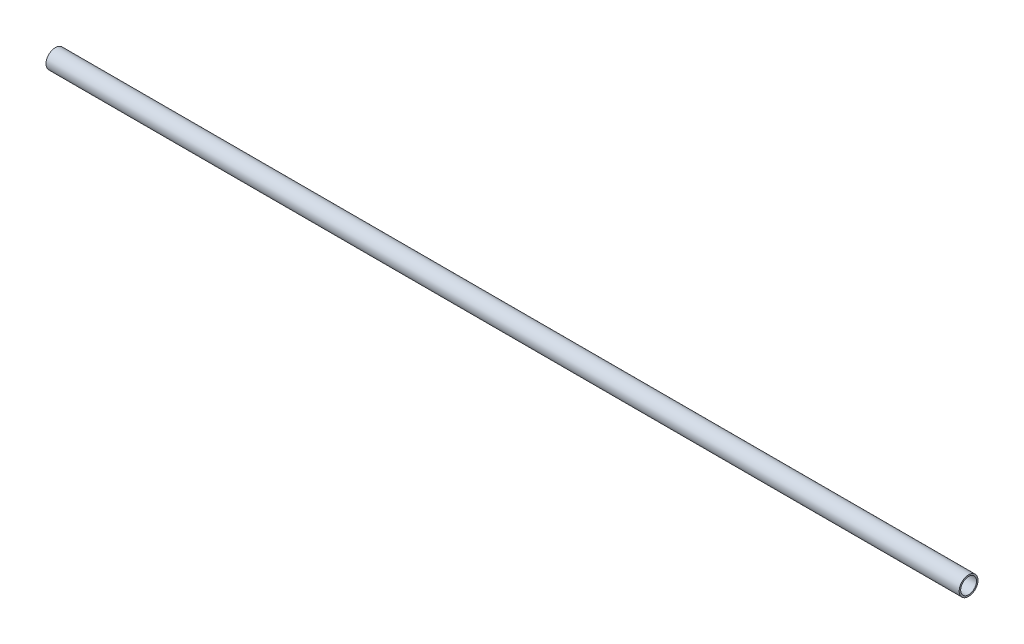
SolidWorks part; units mm, degrees
ref_plane "Front Plane" through (0, 0, 0) normal (0, 0, 1) x (1, 0, 0)
ref_plane "Top Plane" through (0, 0, 0) normal (0, 1, 0) x (1, 0, 0)
ref_plane "Right Plane" through (0, 0, 0) normal (1, 0, 0) x (0, 0, -1)
sketch "Sketch1" plane through (0, 0, 0) normal (1, 0, 0) x (0, 0, -1)
  circle A0 centre (0, 0) radius 3.175
  circle A1 centre (0, 0) radius 2.667
  dimension "D1" = 6.35
  dimension "D2" = 0.508
extrude "Boss-Extrude1" add sketch "Sketch1" against normal blind 307.975
